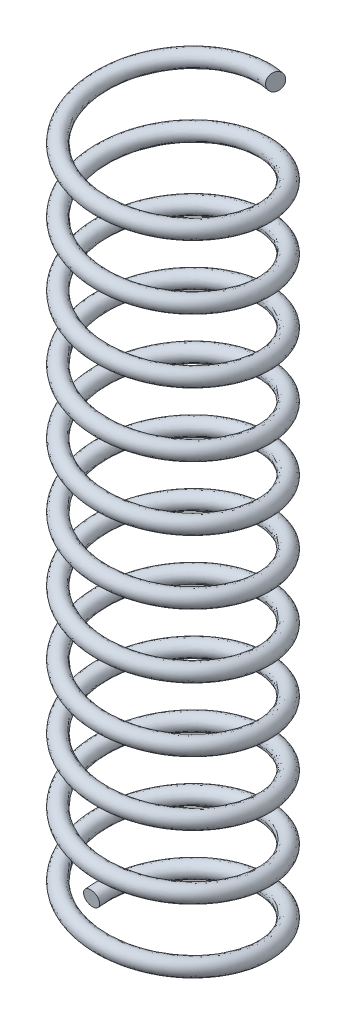
SolidWorks part; units mm, degrees
ref_plane "Front Plane" through (0, 0, 0) normal (0, 0, 1) x (1, 0, 0)
ref_plane "Top Plane" through (0, 0, 0) normal (0, 1, 0) x (1, 0, 0)
ref_plane "Right Plane" through (0, 0, 0) normal (1, 0, 0) x (0, 0, -1)
sketch "Sketch1" plane through (0, 0, 0) normal (0, 1, 0) x (1, 0, 0)
  circle A0 centre (0, 0) radius 2.55
  dimension "D1" = 5.1
curve "Helix/Spiral1" pitch 2 height 22.6 turns 11.3
sweep "Sweep1" add path "Helix/Spiral1" circular profile diameter 0.5 parameters "D3"=0.5
